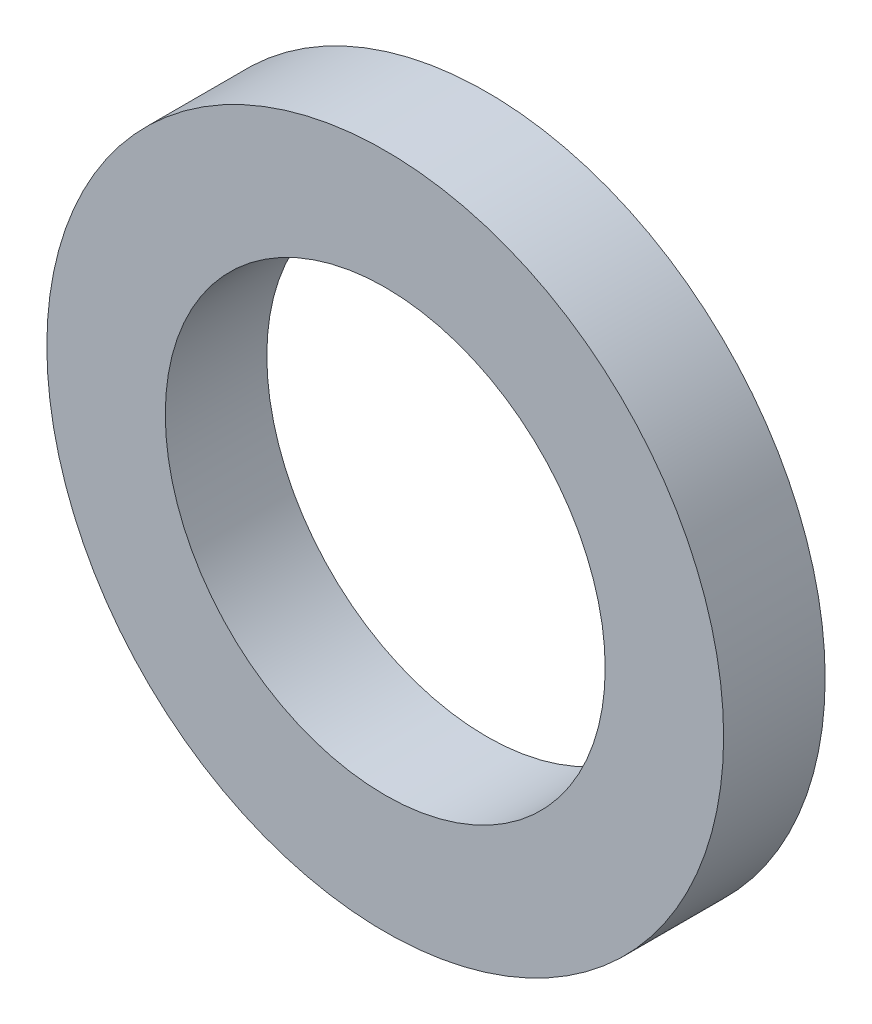
SolidWorks part; units mm, degrees
ref_plane "前视基准面" through (0, 0, 0) normal (0, 0, 1) x (1, 0, 0)
ref_plane "上视基准面" through (0, 0, 0) normal (0, 1, 0) x (1, 0, 0)
ref_plane "右视基准面" through (0, 0, 0) normal (1, 0, 0) x (0, 0, -1)
other "Configuration Table"
sketch "草图1" plane through (0, 0, 0) normal (0, 0, 1) x (1, 0, 0)
  circle A0 centre (0, 0) radius 6.5
  circle A1 centre (0, 0) radius 10
  dimension "D1" = 13
  dimension "D2" = 20
extrude "凸台-拉伸1" add sketch "草图1" along normal blind 3
